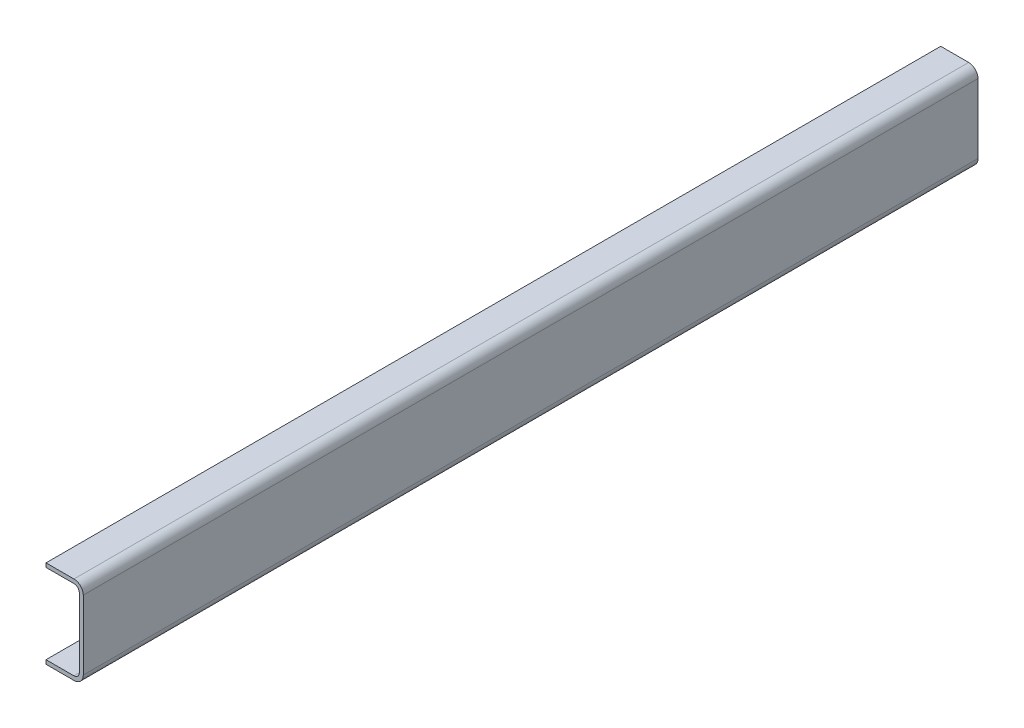
SolidWorks part; units mm, degrees
material "ASTM A572, GR50"
ref_plane "Edge of Rail 1" through (0, 0, 0) normal (0, 0, 1) x (1, 0, 0)
ref_plane "Bottom Flange" through (0, 0, 0) normal (0, 1, 0) x (1, 0, 0)
ref_plane "Outside Web" through (0, 0, 0) normal (1, 0, 0) x (0, 0, -1)
ref_plane "Top Flange" through (0, 209.55, 0) normal (0, 1, 0) x (-1, 0, 0)
ref_plane "Edge of Rail 2" through (0, 0, -2133.6) normal (0, 0, 1) x (1, 0, 0)
ref_plane "Inside Flange Edge" through (-88.9, 0, 0) normal (1, 0, 0) x (0, 0, -1)
sketch "Sketch1" plane through (0, 0, 0) normal (0, 0, 1) x (1, 0, 0)
  line L0 (50, 209.55) -> (-50, 209.55) construction
  line L1 (-88.9, 0) -> (0, 0)
  line L2 (-88.9, -50) -> (-88.9, 50) construction
  line L3 (-88.9, 209.55) -> (0, 209.55)
  line L4 (0, 0) -> (0, 209.55)
extrude "Base-Extrude-Thin" add sketch "Sketch1" against normal up to surface (2133.6 mm away) thin up to plane "Edge of Rail 2" thin type one direction wall 9.525
fillet "Inside Bend Radius" radius 12.7 2 edges at (-9.525, 200.025, -1066.8) (-9.525, 9.525, -1066.8)
fillet "Outside Bend Radius" radius 22.225 2 edges at (0, 0, -1066.8) (0, 209.55, -1066.8)
equation "\"OUTSIDE_RADIUS@Outside Bend Radius\" = \"INSIDE_RADIUS@Inside Bend Radius\"+\"THICKNESS@Base-Extrude-Thin\""
